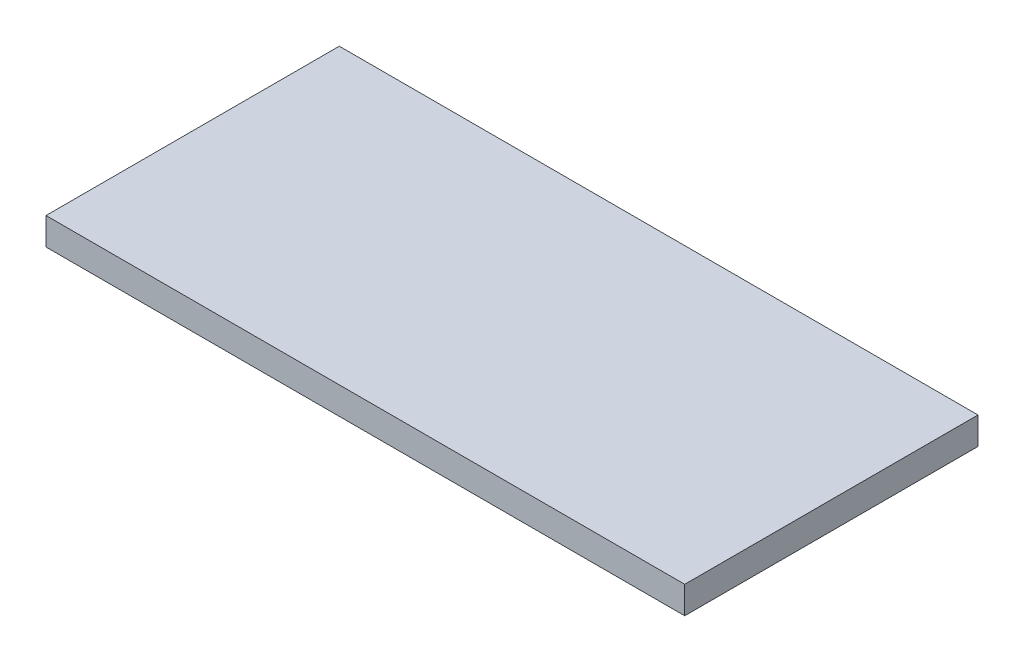
SolidWorks part; units mm, degrees
ref_plane "Front Plane" through (0, 0, 0) normal (0, 0, 1) x (1, 0, 0)
ref_plane "Top Plane" through (0, 0, 0) normal (0, 1, 0) x (1, 0, 0)
ref_plane "Right Plane" through (0, 0, 0) normal (1, 0, 0) x (0, 0, -1)
sketch "Sketch1" plane through (0, 0, 0) normal (0, 1, 0) x (1, 0, 0)
  line L1 (0, 0) -> (36.5, 0)
  line L2 (0, 0) -> (0, 16.76)
  line L3 (0, 16.76) -> (36.5, 16.76)
  line L4 (36.5, 0) -> (36.5, 16.76)
  dimension "D1" = 36.5
  dimension "D2" = 16.76
extrude "Boss-Extrude1" add sketch "Sketch1" along normal blind 1.56 contours L2 L3 L4 L1
